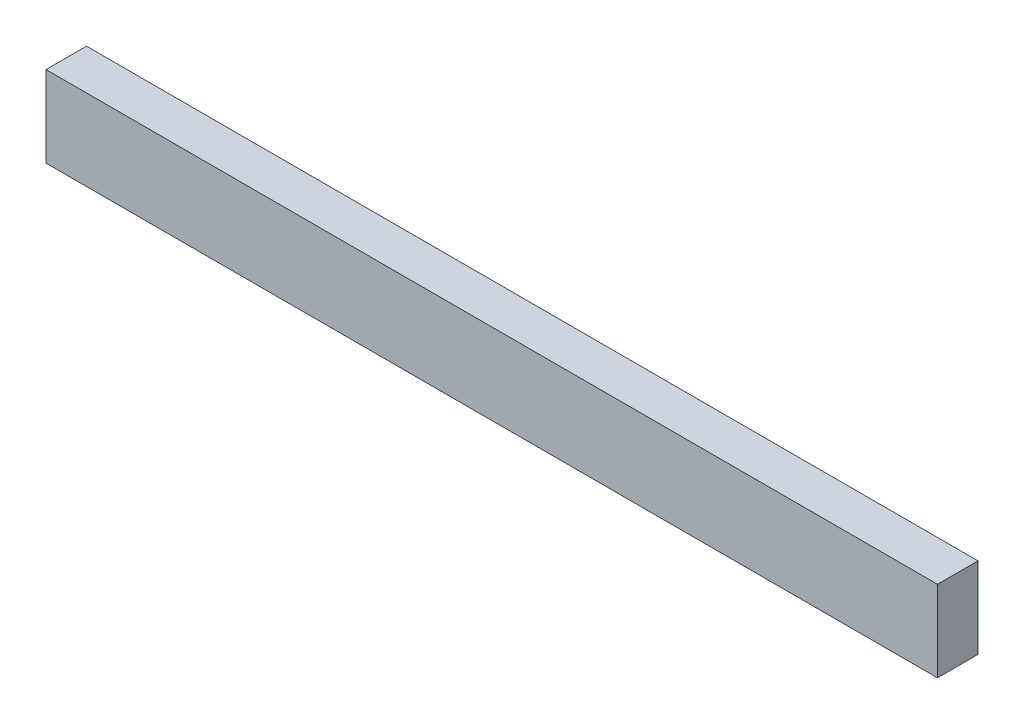
SolidWorks part; units mm, degrees
ref_plane "Front Plane" through (0, 0, 0) normal (0, 0, 1) x (1, 0, 0)
ref_plane "Top Plane" through (0, 0, 0) normal (0, 1, 0) x (1, 0, 0)
ref_plane "Right Plane" through (0, 0, 0) normal (1, 0, 0) x (0, 0, -1)
sketch "Sketch1" plane through (0, 0, 0) normal (0, 0, 1) x (1, 0, 0)
  line L1 (-110, -10) -> (110, -10)
  line L2 (-110, -10) -> (-110, 10)
  line L3 (-110, 10) -> (110, 10)
  line L4 (110, -10) -> (110, 10)
  line L5 (-110, -10) -> (110, 10) construction
  line L6 (-110, 10) -> (110, -10) construction
  point P0 (0, 0)
  dimension "D1" = 220
  dimension "D2" = 20
extrude "Boss-Extrude1" add sketch "Sketch1" along normal blind 10
